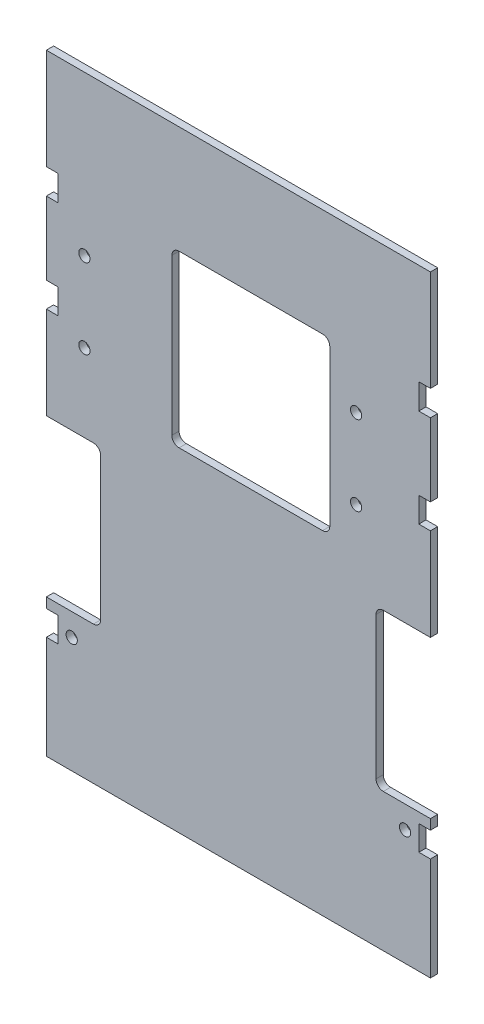
SolidWorks part; units mm, degrees
material "Thornel Mat VMA"
ref_plane "前视基准面" through (0, 0, 0) normal (0, 0, 1) x (1, 0, 0)
ref_plane "上视基准面" through (0, 0, 0) normal (0, 1, 0) x (1, 0, 0)
ref_plane "右视基准面" through (0, 0, 0) normal (1, 0, 0) x (0, 0, -1)
sketch "草图1" plane through (0, 0, 0) normal (0, 0, 1) x (1, 0, 0)
  line L0 (-42.5, 41.5) -> (-42.5, -95.682) construction
  line L2 (-53, 72.5231) -> (-53, 52.406)
  line L4 (53, 67.4845) -> (53, 52.406)
  line L5 (-53, 67.4845) -> (53, -67.4845) construction
  line L6 (-53, -67.4845) -> (53, 67.4845) construction
  line L7 (-53, 79.5409) -> (-53, 107.3845)
  line L9 (53, 107.3845) -> (53, 79.5409)
  line L10 (-53, -61.3845) -> (53, -61.3845)
  line L11 (-16.3692, 77.6578) -> (23.229, 77.6578)
  line L12 (-18.3692, 75.6578) -> (-18.3692, 32.6605)
  line L13 (-16.3692, 30.6605) -> (23.229, 30.6605)
  line L14 (25.229, 75.6578) -> (25.229, 32.6605)
  line L15 (-18.3692, 77.6578) -> (25.229, 30.6605) construction
  line L16 (-18.3692, 30.6605) -> (25.229, 77.6578) construction
  line L17 (-53, 107.3845) -> (53, 107.3845)
  line L18 (53, 20.0116) -> (40, 20.0116)
  line L19 (38, 18.0116) -> (38, -21.289)
  line L20 (40, -23.289) -> (53, -23.289)
  line L21 (53, -23.289) -> (53, -26.0672)
  line L22 (-53, 20.0116) -> (-40, 20.0116)
  line L23 (-38, 18.0116) -> (-38, -21.289)
  line L24 (-40, -23.289) -> (-53, -23.289)
  line L25 (-53, -23.289) -> (-53, -26.0672)
  line L26 (0, 147.2807) -> (0, -147.2807) construction
  line L27 (-53, -26.0672) -> (-49.8, -26.0672)
  line L28 (-49.8, -26.0672) -> (-49.8, -32.9301)
  line L29 (-49.8, -32.9301) -> (-53, -32.9301)
  line L30 (-53, -32.9301) -> (-53, -61.3845)
  line L31 (-53, 52.406) -> (-49.8, 52.406)
  line L32 (-49.8, 52.406) -> (-49.8, 45.5077)
  line L33 (-49.8, 45.5077) -> (-53, 45.5077)
  line L34 (-53, 45.5077) -> (-53, 20.0116)
  line L35 (-53, 79.5409) -> (-49.8, 79.5409)
  line L36 (-49.8, 79.5409) -> (-49.8, 72.5231)
  line L37 (-49.8, 72.5231) -> (-53, 72.5231)
  line L38 (49.8, -32.9301) -> (53, -32.9301)
  line L39 (49.8, -26.0672) -> (49.8, -32.9301)
  line L40 (53, -26.0672) -> (49.8, -26.0672)
  line L41 (49.8, 52.406) -> (49.8, 45.5077)
  line L42 (49.8, 45.5077) -> (53, 45.5077)
  line L43 (53, 52.406) -> (49.8, 52.406)
  line L44 (49.8, 72.5231) -> (53, 72.5231)
  line L45 (49.8, 79.5409) -> (49.8, 72.5231)
  line L46 (53, 79.5409) -> (49.8, 79.5409)
  line L47 (53, 72.5231) -> (53, 67.4845)
  line L48 (53, 45.5077) -> (53, 20.0116)
  line L49 (53, -32.9301) -> (53, -61.3845)
  circle A0 centre (-42.5, 63.5) radius 1.55
  circle A3 centre (32.5, 63.5155) radius 1.55
  circle A4 centre (-42.5, 41.5) radius 1.55
  circle A5 centre (32.5, 41.5155) radius 1.55
  circle A6 centre (-46, -29.4845) radius 1.55
  circle A7 centre (46, -29.4845) radius 1.55
  arc A8 (-16.3692, 77.6578) -> (-18.3692, 75.6578) centre (-16.3692, 75.6578) ccw
  arc A9 (25.229, 75.6578) -> (23.229, 77.6578) centre (23.229, 75.6578) ccw
  arc A10 (25.229, 32.6605) -> (23.229, 30.6605) centre (23.229, 32.6605) cw
  arc A11 (-18.3692, 32.6605) -> (-16.3692, 30.6605) centre (-16.3692, 32.6605) ccw
  arc A12 (40, -23.289) -> (38, -21.289) centre (40, -21.289) cw
  arc A13 (38, 18.0116) -> (40, 20.0116) centre (40, 18.0116) cw
  arc A14 (-40, 20.0116) -> (-38, 18.0116) centre (-40, 18.0116) cw
  arc A15 (-38, -21.289) -> (-40, -23.289) centre (-40, -21.289) cw
  point P0 (0, 0)
  point P8 (3.4299, 54.1592)
  point P52 (38, 20.0116)
  dimension "D2" = 10.5
  dimension "D11" = 3.2
  dimension "D3" = 2
  dimension "D8" = 2
  dimension "D9" = 3.2
  dimension "D1" = 106
  dimension "D4" = 15
  dimension "D5" = 15
  dimension "D6" = 22
  dimension "D7" = 22
  dimension "D10" = 3.2
  dimension "D13" = 7
  dimension "D14" = 7
extrude "凸台-拉伸1" add sketch "草图1" along normal blind 2
